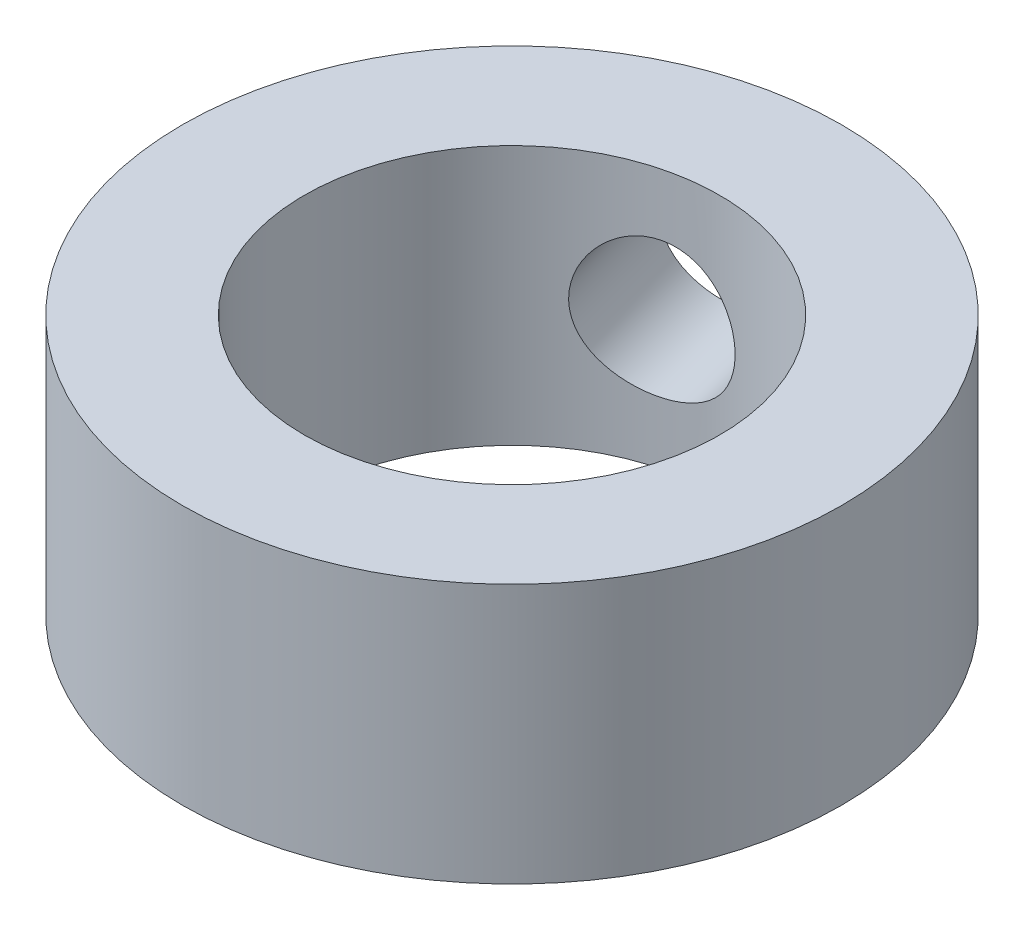
SolidWorks part; units mm, degrees
ref_plane "Front Plane" through (0, 0, 0) normal (0, 0, 1) x (1, 0, 0)
ref_plane "Top Plane" through (0, 0, 0) normal (0, 1, 0) x (1, 0, 0)
ref_plane "Right Plane" through (0, 0, 0) normal (1, 0, 0) x (0, 0, -1)
sketch "Sketch1" plane through (0, 0, 0) normal (0, 1, 0) x (1, 0, 0)
  circle A0 centre (0, 0) radius 25.4
extrude "Boss-Extrude1" add sketch "Sketch1" along normal blind 20
sketch "Sketch2" plane through (0, 20, 0) normal (0, 1, 0) x (1, 0, 0)
  circle A0 centre (0, 0) radius 16
extrude "Cut-Extrude1" cut sketch "Sketch2" against normal through all
hole_wizard "Ø10.5 (10.5) Diameter Hole1" positions "3DSketch1" profile "Sketch3" hole size "Ø10.5" standard "Ansi Metric"
sketch3d "3DSketch1"
  line L0 (0, 0, 0) -> (-6.4569, 0, -24.5656)
  line L1 (-6.4569, 0, -24.5656) -> (-6.4569, 10, -24.5656)
  circle A0 centre (0, 0, 0) radius 25.4 construction
  point P0 (-6.4569, 10, -24.5656)
  point P7 (0, 25.4, 0)
  dimension "D1" = 10
sketch "Sketch3" plane through (-6.4569, 10, -24.5656) normal (0, 1, 0) x (-0.9671, 0, 0.2542)
  line L0 (0, 0) -> (0, 33.1545)
  line L1 (0, 33.1545) -> (5.25, 30)
  line L2 (5.25, 30) -> (5.25, 0)
  line L5 (5.25, 0) -> (0, 0)
  line L10 (0, 33.1545) -> (-5.25, 30) construction
  line L11 (0, -6.35) -> (0, 107.95) construction
  dimension "Hole Dia." = 10.5
  dimension "Hole Depth" = 30
  dimension "Drill Angle" = 118
